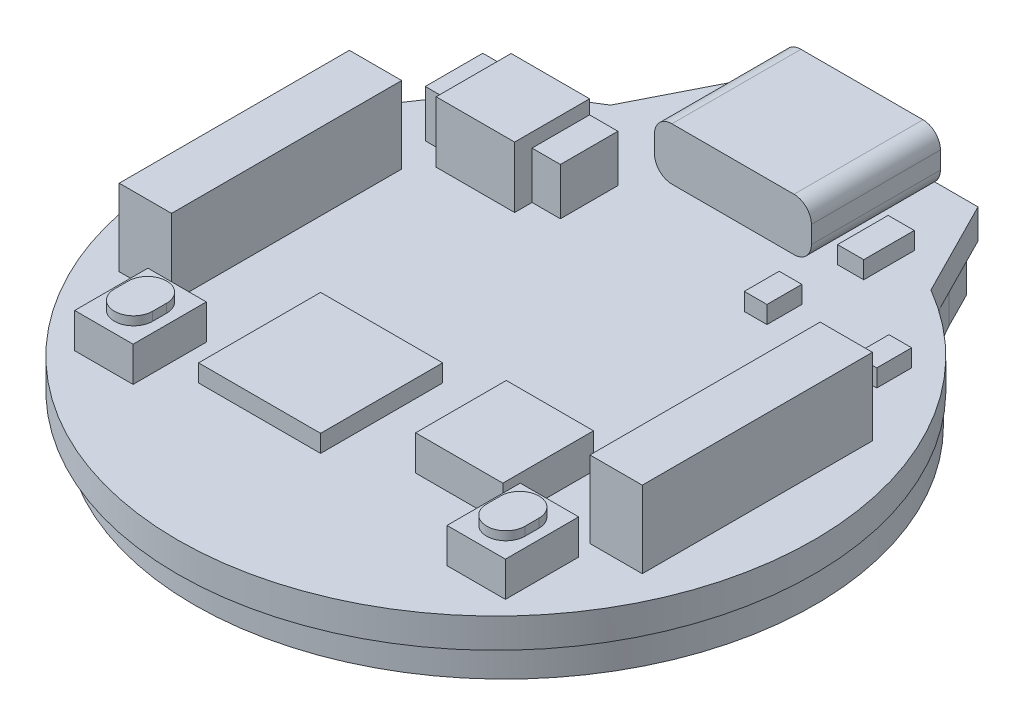
SolidWorks part; units mm, degrees
ref_plane "Front Plane" through (0, 0, 0) normal (0, 0, 1) x (1, 0, 0)
ref_plane "Top Plane" through (0, 0, 0) normal (0, 1, 0) x (1, 0, 0)
ref_plane "Right Plane" through (0, 0, 0) normal (1, 0, 0) x (0, 0, -1)
sketch "Sketch1" plane through (0, 0, 0) normal (0, 1, 0) x (1, 0, 0)
  line L0 (-9.185, 15.7702) -> (9.185, 15.7702) construction
  line L1 (-6.405, 21.2502) -> (6.405, 21.2502)
  line L2 (-6.405, 21.2502) -> (-9.185, 15.7702)
  line L3 (6.405, 21.2502) -> (9.185, 15.7702)
  arc A0 (-9.185, 15.7702) -> (9.185, 15.7702) centre (0, 0) ccw
  point P1 (0, 21.2502)
  dimension "D1" = 36.5
  dimension "D2" = 18.37
  dimension "D3" = 12.81
  dimension "D4" = 5.48
extrude "Boss-Extrude1" add sketch "Sketch1" along normal blind 1.7
sketch "Sketch2" plane through (0, 0, 0) normal (0, 1, 0) x (1, 0, 0)
  line L0 (-6.75, 20.2502) -> (6.75, 20.2502)
  line L3 (6.405, 21.2502) -> (-6.405, 21.2502) construction
  line L4 (-6.75, 20.2502) -> (-7.7944, 18.1915)
  line L5 (-6.405, 21.2502) -> (-9.185, 15.7702) construction
  line L6 (6.75, 20.2502) -> (7.7944, 18.1915)
  line L7 (9.185, 15.7702) -> (6.405, 21.2502) construction
  arc A0 (-10.7008, 14.7244) -> (10.7008, 14.7244) centre (0, 0.5) ccw
  arc A1 (7.7944, 18.1915) -> (10.7008, 14.7244) centre (16.7124, 22.7156) ccw
  arc A2 (-7.7944, 18.1915) -> (-10.7008, 14.7244) centre (-16.7124, 22.7156) cw
  point P10 (0, 20.2502)
  dimension "D1" = 35.6
  dimension "D5" = 10
  dimension "D2" = 0.5
  dimension "D3" = 1
  dimension "D4" = 13.5
extrude "Boss-Extrude2" add sketch "Sketch2" against normal blind 2
sketch "Sketch3" plane through (0, 0, 0) normal (0, 1, 0) x (1, 0, 0)
  line L0 (-13.5, 0) -> (13.5, 0) construction
  line L1 (-15, 6.6) -> (-12, 6.6)
  line L2 (-15, 6.6) -> (-15, -6.6)
  line L3 (-15, -6.6) -> (-12, -6.6)
  line L4 (-12, 6.6) -> (-12, -6.6)
  line L5 (-15, 6.6) -> (-12, -6.6) construction
  line L6 (-15, -6.6) -> (-12, 6.6) construction
  line L7 (12, 6.6) -> (15, 6.6)
  line L8 (12, 6.6) -> (12, -6.6)
  line L9 (12, -6.6) -> (15, -6.6)
  line L10 (15, 6.6) -> (15, -6.6)
  line L11 (12, 6.6) -> (15, -6.6) construction
  line L12 (12, -6.6) -> (15, 6.6) construction
  point P0 (-13.5, 0)
  point P5 (13.5, 0)
  point P13 (0, 0)
  dimension "D1" = 13.2
  dimension "D2" = 3
  dimension "D3" = 27
extrude "Boss-Extrude3" add sketch "Sketch3" along normal blind 4.4 from surface at 1.7 starting at face at (0, 1.7, -10.0051)
sketch "Sketch4" plane through (0, 0, 0) normal (0, 0, 1) x (1, 0, 0)
  line L0 (6.405, 1.7) -> (-6.405, 1.7) construction
  line L1 (3.5, 1.7) -> (-3.5, 1.7)
  line L2 (4.5, 2.7) -> (4.5, 3.7)
  line L3 (3.5, 4.7) -> (-3.5, 4.7)
  line L4 (-4.5, 2.7) -> (-4.5, 3.7)
  line L5 (4.5, 1.7) -> (-4.5, 4.7) construction
  line L6 (4.5, 4.7) -> (-4.5, 1.7) construction
  arc A0 (-3.5, 1.7) -> (-4.5, 2.7) centre (-3.5, 2.7) cw
  arc A1 (-3.5, 4.7) -> (-4.5, 3.7) centre (-3.5, 3.7) ccw
  arc A2 (3.5, 1.7) -> (4.5, 2.7) centre (3.5, 2.7) ccw
  arc A3 (4.5, 3.7) -> (3.5, 4.7) centre (3.5, 3.7) ccw
  point P0 (0, 3.2)
  dimension "D3" = 1
  dimension "D1" = 3
  dimension "D2" = 9
extrude "Boss-Extrude4" add sketch "Sketch4" along normal blind 7.4 from offset 21 offset against normal yes
sketch "Sketch7" plane through (0, 0, 0) normal (0, 0, 1) x (1, 0, 0)
  line L0 (3.5, 4.4) -> (-3.5, 4.4)
  line L1 (-4.2, 3.7) -> (-4.2, 2.7)
  line L2 (-3.5, 2) -> (3.5, 2)
  line L3 (4.2, 2.7) -> (4.2, 3.7)
  line L4 (-4.5, 3.7) -> (-4.5, 2.7)
  line L5 (3.5, 4.7) -> (-3.5, 4.7)
  line L6 (4.5, 2.7) -> (4.5, 3.7)
  line L7 (-3.5, 1.7) -> (3.5, 1.7)
  line L8 (-4.5, 3.7) -> (-4.5, 2.7)
  line L9 (3.5, 4.7) -> (-3.5, 4.7)
  line L10 (4.5, 2.7) -> (4.5, 3.7)
  line L11 (-3.5, 1.7) -> (3.5, 1.7)
  arc A0 (-3.5, 4.4) -> (-4.2, 3.7) centre (-3.5, 3.7) ccw
  arc A1 (-4.2, 2.7) -> (-3.5, 2) centre (-3.5, 2.7) ccw
  arc A2 (3.5, 2) -> (4.2, 2.7) centre (3.5, 2.7) ccw
  arc A3 (4.2, 3.7) -> (3.5, 4.4) centre (3.5, 3.7) ccw
  arc A4 (-4.5, 2.7) -> (-3.5, 1.7) centre (-3.5, 2.7) ccw
  arc A5 (-3.5, 4.7) -> (-4.5, 3.7) centre (-3.5, 3.7) ccw
  arc A6 (4.5, 3.7) -> (3.5, 4.7) centre (3.5, 3.7) ccw
  arc A7 (3.5, 1.7) -> (4.5, 2.7) centre (3.5, 2.7) ccw
  arc A8 (-4.5, 2.7) -> (-3.5, 1.7) centre (-3.5, 2.7) ccw
  arc A9 (-3.5, 4.7) -> (-4.5, 3.7) centre (-3.5, 3.7) ccw
  arc A10 (4.5, 3.7) -> (3.5, 4.7) centre (3.5, 3.7) ccw
  arc A11 (3.5, 1.7) -> (4.5, 2.7) centre (3.5, 2.7) ccw
  dimension "D1" = 0
  dimension "D2" = 0.3
extrude "Cut-Extrude1" cut sketch "Sketch7" along normal blind 6 from surface at -21 contours L3 A3 L0 A0 L1 A1 L2 A2 starting at face at (0, 3.2, -21)
sketch "Sketch8" plane through (0, 0, 0) normal (0, 0, 1) x (1, 0, 0)
  line L0 (3.995, 4.195) -> (-3.995, 2.205) construction
  line L2 (3, 2.875) -> (-3, 2.875)
  line L3 (3, 2.875) -> (3, 3.525)
  line L4 (3, 3.525) -> (-3, 3.525)
  line L5 (-3, 2.875) -> (-3, 3.525)
  line L6 (3, 2.875) -> (-3, 3.525) construction
  line L7 (3, 3.525) -> (-3, 2.875) construction
  arc A0 (4.2, 3.7) -> (3.5, 4.4) centre (3.5, 3.7) ccw construction
  arc A1 (-4.2, 2.7) -> (-3.5, 2) centre (-3.5, 2.7) ccw construction
  point P8 (0, 3.2)
  dimension "D1" = 0.65
  dimension "D2" = 6
extrude "Boss-Extrude5" add sketch "Sketch8" against normal blind 5 from surface at -15 starting at face at (0, 3.2, -15)
fillet "Fillet1" radius 0.5 2 edges at (-3, 3.2, -20) (3, 3.2, -20)
sketch "Sketch9" plane through (0, 0, 0) normal (0, 1, 0) x (1, 0, 0)
  line L0 (12, -6.6) -> (12, 6.6) construction
  line L1 (3.5, -2.9) -> (8.5, -2.9)
  line L2 (3.5, -2.9) -> (3.5, -8.1)
  line L3 (3.5, -8.1) -> (8.5, -8.1)
  line L4 (8.5, -2.9) -> (8.5, -8.1)
  line L5 (3.5, -2.9) -> (8.5, -8.1) construction
  line L6 (3.5, -8.1) -> (8.5, -2.9) construction
  line L7 (15, -6.6) -> (12, -6.6) construction
  point P0 (6, -5.5)
  dimension "D1" = 5.2
  dimension "D2" = 5
  dimension "D3" = 1.5
  dimension "D4" = 3.5
extrude "Boss-Extrude6" add sketch "Sketch9" along normal blind 2 from surface at 1.7 starting at face at (13.5, 1.7, 0)
sketch "Sketch10" plane through (0, 0, 0) normal (0, 1, 0) x (1, 0, 0)
  line L0 (15, -6.6) -> (12, -6.6) construction
  line L1 (9, -7.6) -> (12.35, -7.6)
  line L2 (9, -7.6) -> (9, -11.8)
  line L3 (9, -11.8) -> (12.35, -11.8)
  line L4 (12.35, -7.6) -> (12.35, -11.8)
  line L5 (9, -7.6) -> (12.35, -11.8) construction
  line L6 (9, -11.8) -> (12.35, -7.6) construction
  line L7 (8.5, -2.9) -> (8.5, -8.1) construction
  line L8 (-12.355, -7.6) -> (-9.005, -7.6)
  line L9 (-12.355, -7.6) -> (-12.355, -11.8)
  line L10 (-12.355, -11.8) -> (-9.005, -11.8)
  line L11 (-9.005, -7.6) -> (-9.005, -11.8)
  line L12 (-12.355, -7.6) -> (-9.005, -11.8) construction
  line L13 (-12.355, -11.8) -> (-9.005, -7.6) construction
  point P0 (10.675, -9.7)
  point P10 (-10.68, -9.7)
  dimension "D1" = 4.2
  dimension "D2" = 3.35
  dimension "D3" = 1
  dimension "D4" = 0.5
  dimension "D5" = 10.68
extrude "Boss-Extrude7" add sketch "Sketch10" along normal blind 2 from surface at 1.7 starting at face at (6, 1.7, 5.5)
sketch "Sketch11" plane through (0, 0, 0) normal (0, 1, 0) x (1, 0, 0)
  line L0 (-10.68, -10.1) -> (-10.68, -9.3) construction
  line L1 (-12.355, -11.8) -> (-12.355, -7.6) construction
  line L2 (-11.78, -10.1) -> (-11.78, -9.3)
  line L3 (-9.58, -10.1) -> (-9.58, -9.3)
  line L4 (-12.355, -7.6) -> (-9.005, -7.6) construction
  line L5 (10.675, -10.1) -> (10.675, -9.3) construction
  line L6 (9.575, -10.1) -> (9.575, -9.3)
  line L7 (11.775, -10.1) -> (11.775, -9.3)
  line L8 (9, -11.8) -> (9, -7.6) construction
  line L9 (9, -7.6) -> (12.35, -7.6) construction
  arc A0 (-11.78, -10.1) -> (-9.58, -10.1) centre (-10.68, -10.1) ccw
  arc A1 (-9.58, -9.3) -> (-11.78, -9.3) centre (-10.68, -9.3) ccw
  arc A2 (9.575, -10.1) -> (11.775, -10.1) centre (10.675, -10.1) ccw
  arc A3 (11.775, -9.3) -> (9.575, -9.3) centre (10.675, -9.3) ccw
  point P2 (-10.68, -8.2)
  point P3 (-10.68, -11.2)
  point P4 (-10.68, -9.7)
  point P12 (-12.355, -9.7)
  point P16 (-10.68, -7.6)
  point P19 (10.675, -8.2)
  point P20 (10.675, -11.2)
  point P21 (10.675, -9.7)
  point P29 (9, -9.7)
  point P32 (10.675, -7.6)
  dimension "D1" = 3
  dimension "D2" = 2.2
  dimension "D3" = 3
  dimension "D4" = 2.2
extrude "Boss-Extrude8" add sketch "Sketch11" along normal blind 0.5 from surface at 3.7 starting at face at (-10.68, 3.7, 9.7)
sketch "Sketch12" plane through (0, 0, 0) normal (0, 1, 0) x (1, 0, 0)
  line L1 (-11.1028, 11.9805) -> (-6.6028, 11.9805)
  line L2 (-11.1028, 11.9805) -> (-11.1028, 7.6805)
  line L3 (-11.1028, 7.6805) -> (-6.6028, 7.6805)
  line L4 (-6.6028, 11.9805) -> (-6.6028, 7.6805)
  line L5 (-11.1028, 11.9805) -> (-6.6028, 7.6805) construction
  line L6 (-11.1028, 7.6805) -> (-6.6028, 11.9805) construction
  point P0 (-8.8528, 9.8305)
  dimension "D1" = 4.3
  dimension "D2" = 4.5
extrude "Boss-Extrude9" add sketch "Sketch12" along normal blind 3.5 from surface at 1.7 starting at face at (-10.68, 1.7, 9.7)
sketch "Sketch13" plane through (0, 0, 0) normal (0, 1, 0) x (1, 0, 0)
  line L0 (-11.1028, 11.9805) -> (-6.6028, 11.9805) construction
  line L1 (-12.7278, 8.6805) -> (-4.9778, 8.6805)
  line L2 (-12.7278, 8.6805) -> (-12.7278, 11.9805)
  line L3 (-12.7278, 11.9805) -> (-4.9778, 11.9805)
  line L4 (-4.9778, 8.6805) -> (-4.9778, 11.9805)
  line L5 (-12.7278, 8.6805) -> (-4.9778, 11.9805) construction
  line L6 (-12.7278, 11.9805) -> (-4.9778, 8.6805) construction
  line L7 (-6.6028, 7.6805) -> (-11.1028, 7.6805) construction
  line L8 (-6.6028, 7.6805) -> (-11.1028, 7.6805) construction
  point P0 (-8.8528, 10.3305)
  point P12 (-8.8528, 7.6805)
  dimension "D1" = 1
  dimension "D2" = 7.75
extrude "Boss-Extrude10" add sketch "Sketch13" along normal blind 2.7 from surface at 1.7 starting at face at (-8.8528, 1.7, -9.8305)
sketch "Sketch14" plane through (0, 0, 0) normal (0, 1, 0) x (1, 0, 0)
  line L0 (-12, 6.6) -> (-12, -6.6) construction
  line L1 (-7.2, -2.85) -> (-0.2, -2.85)
  line L2 (-7.2, -2.85) -> (-7.2, -9.85)
  line L3 (-7.2, -9.85) -> (-0.2, -9.85)
  line L4 (-0.2, -2.85) -> (-0.2, -9.85)
  line L5 (-7.2, -2.85) -> (-0.2, -9.85) construction
  line L6 (-7.2, -9.85) -> (-0.2, -2.85) construction
  line L8 (-12, -6.6) -> (-15, -6.6) construction
  point P0 (-3.7, -6.35)
  dimension "D1" = 7
  dimension "D2" = 4.8
  dimension "D3" = 3.25
extrude "Boss-Extrude11" add sketch "Sketch14" along normal blind 1 from surface at 1.7 starting at face at (-8.8528, 1.7, -9.2555)
sketch "Sketch15" plane through (0, 0, 0) normal (0, 1, 0) x (1, 0, 0)
  line L0 (12, 6.6) -> (15, 6.6) construction
  line L1 (11.2, 11.35) -> (12.5, 11.35)
  line L2 (11.2, 11.35) -> (11.2, 9.35)
  line L3 (11.2, 9.35) -> (12.5, 9.35)
  line L4 (12.5, 11.35) -> (12.5, 9.35)
  line L5 (11.2, 11.35) -> (12.5, 9.35) construction
  line L6 (11.2, 9.35) -> (12.5, 11.35) construction
  line L7 (15, 6.6) -> (15, -6.6) construction
  line L9 (4.9, 9.35) -> (6.2, 9.35)
  line L10 (4.9, 9.35) -> (4.9, 11.35)
  line L11 (4.9, 11.35) -> (6.2, 11.35)
  line L12 (6.2, 9.35) -> (6.2, 11.35)
  line L13 (4.9, 9.35) -> (6.2, 11.35) construction
  line L14 (4.9, 11.35) -> (6.2, 9.35) construction
  point P0 (11.85, 10.35)
  point P11 (5.55, 10.35)
  dimension "D1" = 2
  dimension "D2" = 1.3
  dimension "D3" = 2.75
  dimension "D4" = 2.5
  dimension "D5" = 5
extrude "Boss-Extrude12" add sketch "Sketch15" along normal blind 1 from surface at 1.7 starting at face at (-3.7, 1.7, 6.35)
sketch "Sketch16" plane through (0, 0, 0) normal (0, 1, 0) x (1, 0, 0)
  line L0 (-3.5, 13.6) -> (3.5, 13.6) construction
  line L1 (5.25, 17.25) -> (6.75, 17.25)
  line L2 (5.25, 17.25) -> (5.25, 14.35)
  line L3 (5.25, 14.35) -> (6.75, 14.35)
  line L4 (6.75, 17.25) -> (6.75, 14.35)
  line L5 (5.25, 17.25) -> (6.75, 14.35) construction
  line L6 (5.25, 14.35) -> (6.75, 17.25) construction
  line L11 (4.5, 21) -> (3.5, 21)
  line L12 (3.5, 21) -> (3.5, 13.6)
  line L13 (3.5, 13.6) -> (4.5, 13.6)
  line L14 (4.5, 13.6) -> (4.5, 21)
  line L15 (4.5, 21) -> (3.5, 21)
  line L16 (3.5, 21) -> (3.5, 13.6)
  line L17 (3.5, 13.6) -> (4.5, 13.6)
  line L18 (4.5, 13.6) -> (4.5, 21)
  point P0 (6, 15.8)
  dimension "D1" = 2.9
  dimension "D2" = 1.5
  dimension "D3" = 0.75
  dimension "D4" = 0
  dimension "D5" = 0.75
extrude "Boss-Extrude13" add sketch "Sketch16" along normal blind 1 from surface at 1.7 contours L4 L1 L2 L3 starting at face at (5.55, 1.7, -10.35)
move or copy body "Body-Move/Copy2" bodies to move or copy 114 copy no translate (0, -15.7547, 0) parameters "D1"=0, "D2"=15.7547, "D3"=0
